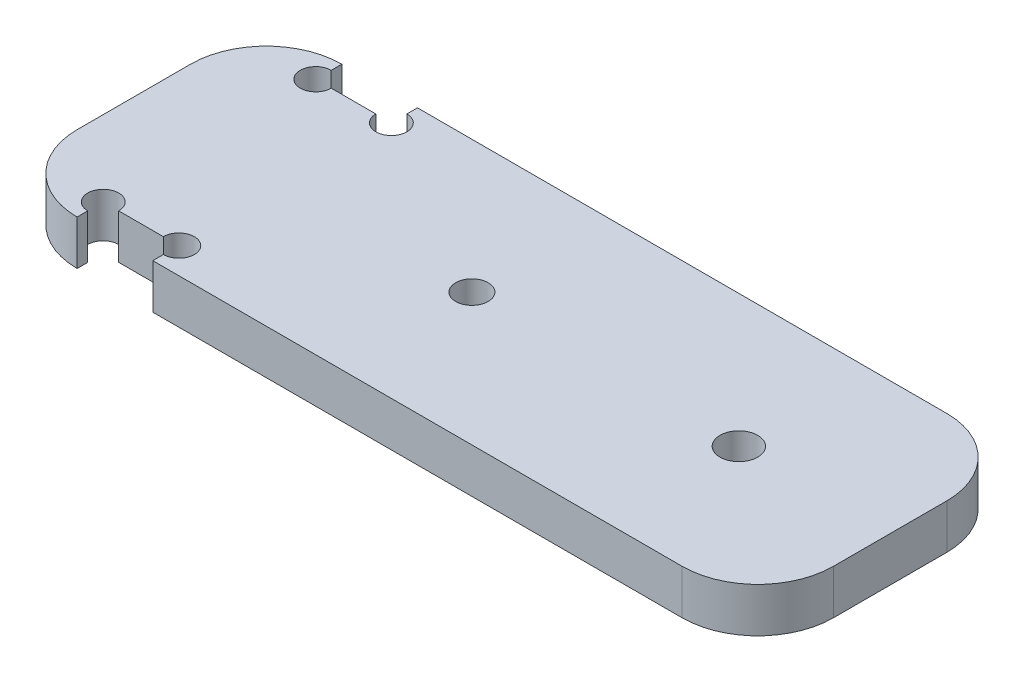
SolidWorks part; units mm, degrees
ref_plane "Front Plane" through (0, 0, 0) normal (0, 0, 1) x (1, 0, 0)
ref_plane "Top Plane" through (0, 0, 0) normal (0, 1, 0) x (1, 0, 0)
ref_plane "Right Plane" through (0, 0, 0) normal (1, 0, 0) x (0, 0, -1)
sketch "Sketch1" plane through (0, 0, 0) normal (0, 1, 0) x (1, 0, 0)
  line L1 (-50, -17.5) -> (50, -17.5)
  line L2 (-50, -17.5) -> (-50, 17.5)
  line L3 (-50, 17.5) -> (50, 17.5)
  line L4 (50, -17.5) -> (50, 17.5)
  line L5 (-50, -17.5) -> (50, 17.5) construction
  line L6 (-50, 17.5) -> (50, -17.5) construction
  point P0 (0, 0)
  dimension "D1" = 35
  dimension "D2" = 100
extrude "Boss-Extrude1" add sketch "Sketch1" along normal blind 5.9
sketch "Sketch2" plane through (0, 5.9, 0) normal (0, 1, 0) x (1, 0, 0)
  line L0 (50, -17.5) -> (50, 17.5) construction
  circle A0 centre (30, 0) radius 2.5
  dimension "D1" = 5
  dimension "D2" = 20
extrude "Cut-Extrude1" cut sketch "Sketch2" against normal blind 10
fillet "Fillet1" radius 10 4 edges at (-50, 2.95, -17.5) (50, 2.95, -17.5) (50, 2.95, 17.5) (-50, 2.95, 17.5)
sketch "Sketch4" plane through (0, 5.9, 0) normal (0, 1, 0) x (1, 0, 0)
  line L0 (40, 17.5) -> (-40, 17.5) construction
  line L1 (-40, 17.5) -> (-30, 17.5)
  line L2 (-40, 17.5) -> (-40, 14.05)
  line L3 (-40, 14.05) -> (-30, 14.05)
  line L4 (-30, 17.5) -> (-30, 14.05)
  line L5 (-50, 7.5) -> (-50, -7.5) construction
  line L6 (0, 0) -> (-50, 0) construction
  line L7 (-40, -14.05) -> (-30, -14.05)
  line L8 (-30, -17.5) -> (-30, -14.05)
  line L9 (-40, -17.5) -> (-30, -17.5)
  line L10 (-40, -17.5) -> (-40, -14.05)
  dimension "D1" = 10
  dimension "D2" = 10
  dimension "D3" = 3.45
extrude "Cut-Extrude3" cut sketch "Sketch4" against normal blind 10
sketch "Sketch5" plane through (0, 5.9, 0) normal (0, 1, 0) x (1, 0, 0)
  line L0 (0, 0) -> (-50, 0) construction
  line L1 (-50, 7.5) -> (-50, -7.5) construction
  circle A0 centre (-5.3, 0) radius 2.15
  dimension "D1" = 4.3
  dimension "D2" = 44.7
extrude "Cut-Extrude5" cut sketch "Sketch5" against normal up to next
sketch "Sketch6" plane through (0, 5.9, 0) normal (0, 1, 0) x (1, 0, 0)
  circle A0 centre (-40, 14.05) radius 2.05
  circle A1 centre (-30, 14.05) radius 2.05
  circle A2 centre (-30, -14.05) radius 2.05
  circle A3 centre (-40, -14.05) radius 2.05
  dimension "D1" = 4.1
extrude "Cut-Extrude6" cut sketch "Sketch6" against normal up to next
equation "\"e\" = 5.9"
equation "\"D1@Boss-Extrude1\"=\"e\""
equation "\"D3@Sketch4\"= 0.5 + 0.5 * \"e\""
